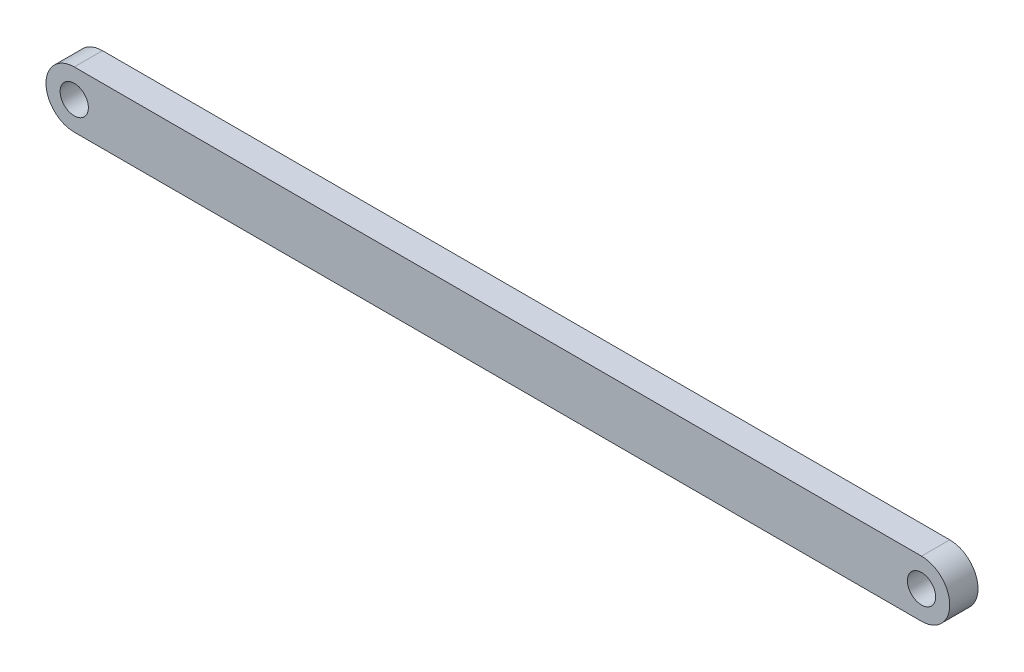
SolidWorks part; units mm, degrees
ref_plane "Front Plane" through (0, 0, 0) normal (0, 0, 1) x (1, 0, 0)
ref_plane "Top Plane" through (0, 0, 0) normal (0, 1, 0) x (1, 0, 0)
ref_plane "Right Plane" through (0, 0, 0) normal (1, 0, 0) x (0, 0, -1)
sketch "Sketch1" plane through (0, 0, 0) normal (0, 0, 1) x (1, 0, 0)
  line L0 (0, -5) -> (0, 5) construction
  line L1 (-75, 5) -> (75, 5)
  line L2 (-75, 5) -> (-75, -5) construction
  line L3 (-75, -5) -> (75, -5)
  line L4 (75, 5) -> (75, -5) construction
  line L5 (-75, 5) -> (75, -5) construction
  line L6 (-75, -5) -> (75, 5) construction
  arc A0 (-75, 5) -> (-75, -5) centre (-75, 0) ccw
  arc A1 (75, 5) -> (75, -5) centre (75, 0) cw
  circle A2 centre (-75, 0) radius 2.5
  circle A3 centre (75, 0) radius 2.5
  point P0 (0, 0)
  dimension "D3" = 5
  dimension "D1" = 10
  dimension "D2" = 150
extrude "Boss-Extrude1" add sketch "Sketch1" along normal blind 5
